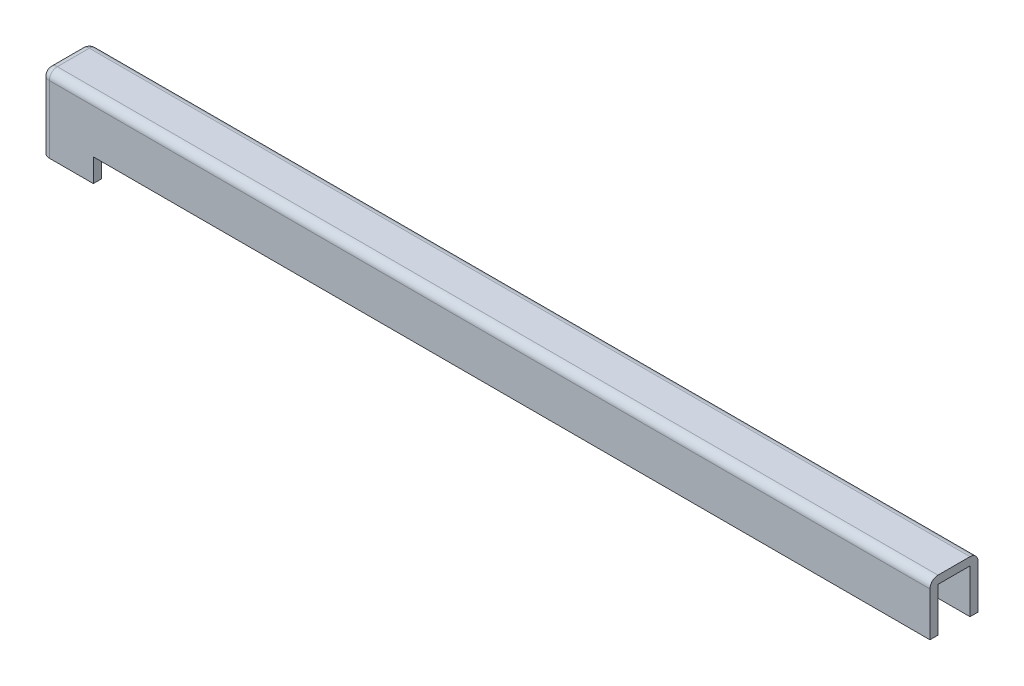
SolidWorks part; units mm, degrees
material "ABS"
ref_plane "Front Plane" through (0, 0, 0) normal (0, 0, 1) x (1, 0, 0)
ref_plane "Top Plane" through (0, 0, 0) normal (0, 1, 0) x (1, 0, 0)
ref_plane "Right Plane" through (0, 0, 0) normal (1, 0, 0) x (0, 0, -1)
sketch "Sketch1" plane through (0, 0, 0) normal (1, 0, 0) x (0, 0, -1)
  line L0 (-2, 0) -> (-2, 13)
  line L1 (0, 0) -> (8, 0)
  line L2 (0, 0) -> (0, 11)
  line L3 (0, 11) -> (8, 11)
  line L4 (8, 0) -> (8, 11)
  line L5 (4, 11) -> (4, 0) construction
  line L6 (0, 5.5) -> (8, 5.5) construction
  line L7 (-2, 13) -> (10, 13)
  line L8 (10, 0) -> (10, 13)
  line L10 (0, 0) -> (-2, 0)
  line L11 (8, 0) -> (10, 0)
  line L12 (-2, -2) -> (-2, 13) construction
  line L13 (-2, -2) -> (10, -2) construction
  line L14 (10, -2) -> (10, 13) construction
  point P156 (4, 5.5)
  dimension "D1" = 8
  dimension "D2" = 11
  dimension "D3" = 2
extrude "Boss-Extrude1" add sketch "Sketch1" along normal blind 220 contours L4 L11 L8 L7 L0 L10 L2 L3
sketch "Sketch2" plane through (0, 0, 0) normal (-1, 0, 0) x (0, 0, 1)
  line L1 (-10, 0) -> (2, 0)
  line L2 (-10, 0) -> (-10, 13)
  line L3 (-10, 13) -> (2, 13)
  line L4 (2, 0) -> (2, 13)
  line L5 (-4, 13) -> (-4, 0) construction
  line L6 (-10, 6.5) -> (2, 6.5) construction
  point P176 (-4, 6.5)
extrude "Boss-Extrude2" add sketch "Sketch2" along normal blind 2
sketch "Sketch4" plane through (0, 0, 0) normal (0, -1, 0) x (1, 0, 0)
  line L0 (11, 0) -> (11, -8)
  line L1 (11, 0) -> (11, 2)
  line L2 (11, -8) -> (11, -10)
  line L8 (220, 2) -> (-2, 2)
  line L9 (-2, 2) -> (-2, -10)
  line L10 (-2, -10) -> (220, -10)
  line L11 (220, -10) -> (220, -8)
  line L12 (220, -8) -> (0, -8)
  line L13 (0, -8) -> (0, 0)
  line L14 (0, 0) -> (220, 0)
  line L15 (220, 0) -> (220, 2)
  line L16 (11, 2) -> (-2, 2)
  line L17 (-2, 2) -> (-2, -10)
  line L18 (-2, -10) -> (11, -10)
  line L20 (11, -8) -> (0, -8)
  line L21 (0, -8) -> (0, 0)
  line L22 (0, 0) -> (11, 0)
  line M10 (220, 2) -> (-2, 2)
  line M11 (-2, 2) -> (-2, -10)
  line M12 (-2, -10) -> (220, -10)
  line M14 (220, -8) -> (0, -8)
  line M15 (0, -8) -> (0, 0)
  line M16 (0, 0) -> (220, 0)
  dimension "D2" = 11
  dimension "D1" = 0
extrude "Boss-Extrude3" add sketch "Sketch4" along normal blind 5.8 contours L2 L1 M14 M15 M16 M10 M11 M12
fillet "Fillet1" radius 2 5 edges at (-2, 3.6, 2) (-2, 13, -4) (109, 13, -10) (109, 13, 2) (-2, 3.6, -10)
